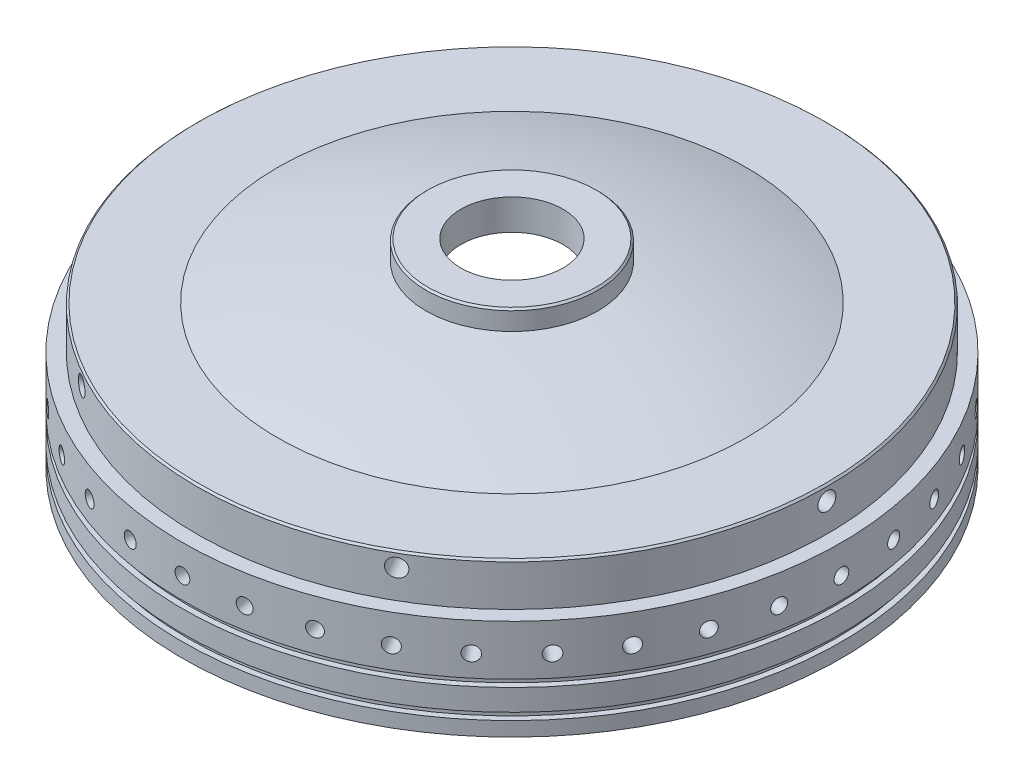
SolidWorks part; units mm, degrees
material "6061-T6 (SS)"
ref_plane "Front Plane" through (0, 0, 0) normal (0, 0, 1) x (1, 0, 0)
ref_plane "Top Plane" through (0, 0, 0) normal (0, 1, 0) x (1, 0, 0)
ref_plane "Right Plane" through (0, 0, 0) normal (1, 0, 0) x (0, 0, -1)
sketch "Sketch1" plane through (0, 0, 0) normal (0, 0, 1) x (1, 0, 0)
  line L0 (0, 81.7273) -> (0, 75.3773)
  line L1 (136.525, 0) -> (146.05, 0)
  line L2 (146.05, 0) -> (146.05, 6.35)
  line L4 (139.6229, 44.45) -> (146.05, 44.45)
  line L5 (130.81, 22.225) -> (130.81, 44.45)
  line L6 (146.05, 6.35) -> (143.51, 6.35)
  line L7 (103.8227, 63.5) -> (139.6229, 63.5)
  line L8 (143.51, 6.35) -> (143.51, 9.525)
  line L9 (143.51, 9.525) -> (146.05, 9.525)
  line L10 (146.05, 19.05) -> (143.51, 19.05)
  line L11 (143.51, 19.05) -> (143.51, 22.225)
  line L12 (143.51, 22.225) -> (146.05, 22.225)
  line L13 (146.05, 9.525) -> (146.05, 19.05)
  line L14 (146.05, 22.225) -> (146.05, 44.45)
  line L15 (139.6229, 63.5) -> (139.6229, 44.45)
  line L17 (136.525, 0) -> (136.525, 22.225)
  line L18 (136.525, 22.225) -> (130.81, 22.225)
  arc A0 (103.8227, 63.5) -> (0, 81.7273) centre (0, -223.0727) ccw
  arc A1 (130.81, 44.45) -> (0, 75.3773) centre (0, -216.7227) ccw
  point P4 (0, 0)
  dimension "D5" = 146.05
  dimension "D1" = 304.8
  dimension "D7" = 3.175
  dimension "D9" = 292.1
  dimension "D10" = 2.54
  dimension "D2" = 6.4271
  dimension "D3" = 9.525
  dimension "D6" = 44.45
  dimension "D8" = 6.35
  dimension "D11" = 6.35
  dimension "D12" = 19.05
  dimension "D13" = 19.05
  dimension "D15" = 15.24
revolve "Revolve1" add sketch "Sketch1" angle 360 about L0
ref_plane "Plane1" through (0, 81.7273, 0) normal (0, 1, 0) x (1, 0, 0)
sketch "Sketch2" plane through (0, 81.7273, 0) normal (0, 1, 0) x (1, 0, 0)
  circle A0 centre (0, 0) radius 38.1
  dimension "D1" = 76.2
extrude "Boss-Extrude1" add sketch "Sketch2" along normal blind 6.35 and the other way up to next
ref_plane "Plane2" through (-146.05, 0, 0) normal (-1, 0, 0) x (0, 0, 1)
hole_wizard "5/16-18 Tapped Hole1" positions "Sketch3" profile "Sketch5" tap size "5/16-18" standard "ANSI Inch"
sketch "Sketch3" plane through (-146.05, 0, 0) normal (-1, 0, 0) x (0, 0, 1)
  line L0 (0, 31.75) -> (0, 0) construction
  line L2 (146.05, 44.45) -> (-146.05, 44.45) construction
  point P0 (0, 31.75)
  dimension "D1" = 12.7
cosmetic thread "Hole Thread1" parameters "D1"=10.16, "D2"=7.9375
sketch "Sketch5" plane through (-146.05, 31.75, 0) normal (0, 1, 0) x (0, 0, 1)
  line L0 (0, 0) -> (0, 14.6611)
  line L1 (0, 14.6611) -> (3.2639, 12.7)
  line L2 (3.2639, 12.7) -> (3.2639, 0)
  line L5 (3.2639, 0) -> (0, 0)
  line L10 (0, 14.6611) -> (-3.2639, 12.7) construction
  line L11 (0, -6.35) -> (0, 107.95) construction
  dimension "Tap Drill Dia." = 6.5278
  dimension "Tap Drill Depth" = 12.7
  dimension "Drill Angle" = 118
pattern_circular "CirPattern1" count 36 over 360 about axis through (0, 44.45, 0) along (0, 1, 0) of "5/16-18 Tapped Hole1"
ref_plane "Plane3" through (-139.6229, 0, 0) normal (-1, 0, 0) x (0, 0, 1)
hole_wizard "3/8-16 Tapped Hole2" positions "Sketch6" profile "Sketch7" tap size "3/8-16" standard "ANSI Inch"
sketch "Sketch6" plane through (-139.6229, 0, 0) normal (-1, 0, 0) x (0, 0, 1)
  line L0 (0, 0) -> (0, 57.15) construction
  line L3 (146.05, 44.45) -> (-146.05, 44.45) construction
  point P0 (0, 57.15)
  dimension "D1" = 12.7
sketch "Sketch7" plane through (-139.6229, 57.15, 0) normal (0, 1, 0) x (0, 0, 1)
  line L0 (0, 0) -> (0, 26.2607)
  line L1 (0, 26.2607) -> (3.9687, 23.876)
  line L2 (3.9687, 23.876) -> (3.9687, 0)
  line L5 (3.9687, 0) -> (0, 0)
  line L10 (0, 26.2607) -> (-3.9688, 23.876) construction
  line L11 (0, -6.35) -> (0, 107.95) construction
  dimension "Tap Drill Dia." = 7.9375
  dimension "Tap Drill Depth" = 23.876
  dimension "Drill Angle" = 118
cosmetic thread "Hole Thread4" parameters "D1"=19.05, "D2"=9.525
hole_wizard "2-4.5 Tapped Hole1" positions "Sketch8" profile "Sketch9" tap size "2-4.5" standard "ANSI Inch"
sketch "Sketch8" plane through (0, 88.0773, 0) normal (0, 1, 0) x (1, 0, 0)
  point P0 (0, 0)
sketch "Sketch9" plane through (0, 88.0773, 0) normal (1, 0, 0) x (0, 0, 1)
  line L0 (0, 0) -> (0, 132.2102)
  line L1 (0, 132.2102) -> (22.6212, 118.618)
  line L2 (22.6212, 118.618) -> (22.6212, 0)
  line L5 (22.6212, 0) -> (0, 0)
  line L10 (0, 132.2102) -> (-22.6212, 118.618) construction
  line L11 (0, -6.35) -> (0, 107.95) construction
  dimension "Tap Drill Dia." = 45.2425
  dimension "Tap Drill Depth" = 118.618
  dimension "Drill Angle" = 118
cosmetic thread "Hole Thread3" parameters "D1"=19.9273, "D2"=50.8
chamfer "Chamfer2" distance 0.7937 angle 45 2 edges at (-38.1, 88.0773, 0) (-139.6229, 63.5, 0)
pattern_circular "CirPattern2" count 6 over 360 about axis through (0, 63.5, 0) along (0, -1, 0) of "3/8-16 Tapped Hole2"
